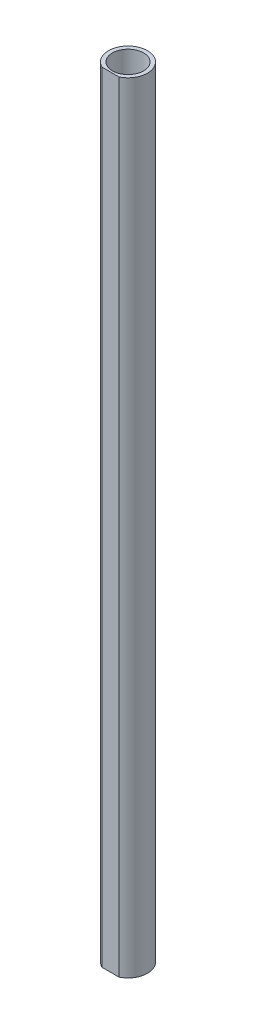
SolidWorks part; units mm, degrees
ref_plane "Front Plane" through (0, 0, 0) normal (0, 0, 1) x (1, 0, 0)
ref_plane "Top Plane" through (0, 0, 0) normal (0, 1, 0) x (1, 0, 0)
ref_plane "Right Plane" through (0, 0, 0) normal (1, 0, 0) x (0, 0, -1)
sketch "Sketch1" plane through (0, 0, 0) normal (0, 1, 0) x (1, 0, 0)
  circle A0 centre (0, 0) radius 20
  circle A1 centre (0, 0) radius 25
  dimension "D1" = 40
  dimension "D2" = 50
extrude "Boss-Extrude1" add sketch "Sketch1" along normal blind 1000
sketch "Sketch2" plane through (0, 1000, 0) normal (0, 1, 0) x (1, 0, 0)
  line L0 (-10.8972, -22.5) -> (10.8972, -22.5)
  circle A0 centre (0, 0) radius 25 construction
  point P2 (-10.8972, -22.5)
  point P6 (10.8972, -22.5)
  dimension "D1" = 22.5
extrude "Cut-Extrude1" cut sketch "Sketch2" against normal through all and the other way through all flip side to cut
